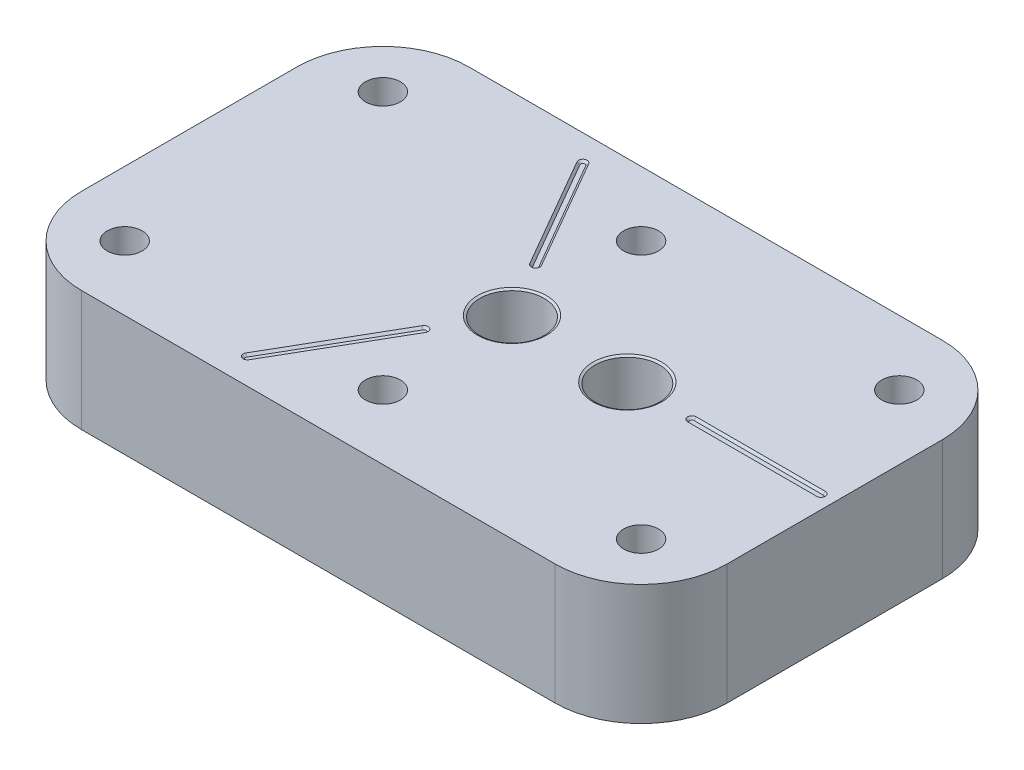
SolidWorks part; units mm, degrees
material "304 SSTL"
ref_plane "Front" through (0, 0, 0) normal (0, 0, 1) x (1, 0, 0)
ref_plane "Top" through (0, 0, 0) normal (0, 1, 0) x (1, 0, 0)
ref_plane "Right" through (0, 0, 0) normal (1, 0, 0) x (0, 0, -1)
sketch "Sketch1" plane through (0, 0, 0) normal (0, 1, 0) x (1, 0, 0)
  line L1 (-95.25, 57.15) -> (95.25, 57.15)
  line L2 (-95.25, 57.15) -> (-95.25, -57.15)
  line L3 (-95.25, -57.15) -> (95.25, -57.15)
  line L4 (95.25, 57.15) -> (95.25, -57.15)
  line L5 (-95.25, 57.15) -> (95.25, -57.15) construction
  line L6 (-95.25, -57.15) -> (95.25, 57.15) construction
  point P0 (0, 0)
  dimension "D1" = 114.3
  dimension "D2" = 190.5
extrude "Extrude1" add sketch "Sketch1" along normal blind 35.56
hole_wizard "3/8 Clearance Hole1" positions "Sketch3" profile "Sketch2" hole size "3/8" standard "Ansi Inch" end condition through all
sketch "Sketch3" plane through (0, 35.56, 0) normal (0, 1, 0) x (-1, 0, 0)
  point P0 (76.2, -38.1)
  dimension "D1" = 76.2
  dimension "D2" = 38.1
sketch "Sketch2" plane through (-76.2, 35.56, -38.1) normal (1, 0, 0) x (0, 0, 1)
  line L0 (0, 0) -> (0, 35.56)
  line L1 (0, 35.56) -> (5.1587, 35.56)
  line L2 (5.1587, 35.56) -> (5.1587, 0)
  line L5 (5.1587, 0) -> (0, 0)
  line L11 (0, -6.35) -> (0, 107.95) construction
  dimension "Thru Hole Dia." = 10.3175
  dimension "Thru Hole Depth" = 35.56
pattern_linear "LPattern6" count 3 spacing 76.2 along (1, 0, 0) count 2 spacing 76.2 along (0, 0, 1) of "3/8 Clearance Hole1"
hole_wizard "5/8-11 Tapped Hole1" positions "Sketch5" profile "Sketch4" tap size "5/8-11" standard "Ansi Inch" end condition through all
sketch "Sketch5" plane through (0, 35.56, 0) normal (0, 1, 0) x (-1, 0, 0)
  point P0 (0, 0)
  point P3 (-34.036, 0)
  dimension "D1" = 34.036
sketch "Sketch4" plane through (0, 35.56, 0) normal (1, 0, 0) x (0, 0, 1)
  line L0 (0, 0) -> (0, 35.56)
  line L1 (0, 35.56) -> (7.9375, 35.56)
  line L2 (7.9375, 35.56) -> (7.9375, 0.3666)
  line L3 (7.9375, 0.3666) -> (8.5725, 0)
  line L5 (8.5725, 0) -> (0, 0)
  line L6 (-7.9375, 0.3666) -> (-8.5725, 0) construction
  line L11 (0, -6.35) -> (0, 107.95) construction
  dimension "Thread Major Dia." = 15.875
  dimension "Thru Tap Drill Depth" = 35.56
  dimension "Near C'Sink Dia." = 17.145
  dimension "Near C'Sink Angle" = 120
fillet "Fillet1" radius 25.4 4 edges at (95.25, 17.78, -57.15) (95.25, 17.78, 57.15) (-95.25, 17.78, 57.15) (-95.25, 17.78, -57.15)
sketch "Sketch6" plane through (0, 35.56, 0) normal (0, 1, 0) x (1, 0, 0)
  line L0 (-9.525, 16.4978) -> (-28.575, 49.4934) construction
  line L1 (-9.525, -16.4978) -> (-28.575, -49.4934) construction
  line L2 (53.086, 0) -> (91.186, 0) construction
  line L3 (-8.4251, 17.1328) -> (-27.4751, 50.1284)
  line L4 (-10.6249, -15.8628) -> (-29.6749, -48.8584)
  line L5 (53.086, -1.27) -> (91.186, -1.27)
  line L6 (-10.6249, 15.8628) -> (-29.6749, 48.8584)
  line L7 (-8.4251, -17.1328) -> (-27.4751, -50.1284)
  line L8 (53.086, 1.27) -> (91.186, 1.27)
  circle A0 centre (34.036, 0) radius 8.5725 construction
  arc A1 (-8.4251, 17.1328) -> (-10.6249, 15.8628) centre (-9.525, 16.4978) cw
  arc A2 (-27.4751, 50.1284) -> (-29.6749, 48.8584) centre (-28.575, 49.4934) ccw
  arc A3 (-10.6249, -15.8628) -> (-8.4251, -17.1328) centre (-9.525, -16.4978) cw
  arc A4 (-29.6749, -48.8584) -> (-27.4751, -50.1284) centre (-28.575, -49.4934) ccw
  arc A5 (53.086, -1.27) -> (53.086, 1.27) centre (53.086, 0) cw
  arc A6 (91.186, -1.27) -> (91.186, 1.27) centre (91.186, 0) ccw
  dimension "D1" = 120
  dimension "D2" = 38.1
  dimension "D3" = 19.05
  dimension "D4" = 19.05
  dimension "D5" = 19.05
  dimension "D8" = 120
  dimension "D6" = 1.27
  dimension "D7" = 1.27
extrude "Extrude2" cut sketch "Sketch6" against normal blind 0.635 draft 45
hole_wizard "Tapped Hole for 5/8-11 Helicoil2" positions "Sketch10" profile "Sketch9" tap size "5/8-11" standard "Helicoil® Inch"
sketch "Sketch10" plane through (0, 35.56, 0) normal (0, 1, 0) x (-1, 0, 0)
  point P0 (0, 0)
  point P3 (-34.036, 0)
sketch "Sketch9" plane through (0, 35.56, 0) normal (1, 0, 0) x (0, 0, 1)
  line L0 (0, 0) -> (0, 43.0566)
  line L1 (0, 43.0566) -> (8.3337, 38.0492)
  line L2 (8.3337, 38.0492) -> (8.3337, 27.7876)
  line L3 (8.3337, 27.7876) -> (9.4958, 27.7876)
  line L5 (9.4958, 27.7876) -> (9.4958, 0.3835)
  line L6 (9.4958, 0.3835) -> (10.16, 0)
  line L7 (10.16, 0) -> (0, 0)
  line L8 (-9.4958, 0.3835) -> (-10.16, 0) construction
  line L10 (0, 43.0566) -> (-8.3337, 38.0492) construction
  line L11 (0, -6.35) -> (0, 107.95) construction
  dimension "Tap Drill Dia." = 16.6675
  dimension "Tap Drill Depth" = 38.0492
  dimension "Thread Major Dia." = 18.9916
  dimension "Thread Depth" = 27.7876
  dimension "Near C'Sink Dia." = 20.32
  dimension "Near C'Sink Angle" = 120
  dimension "Drill Angle" = 118
